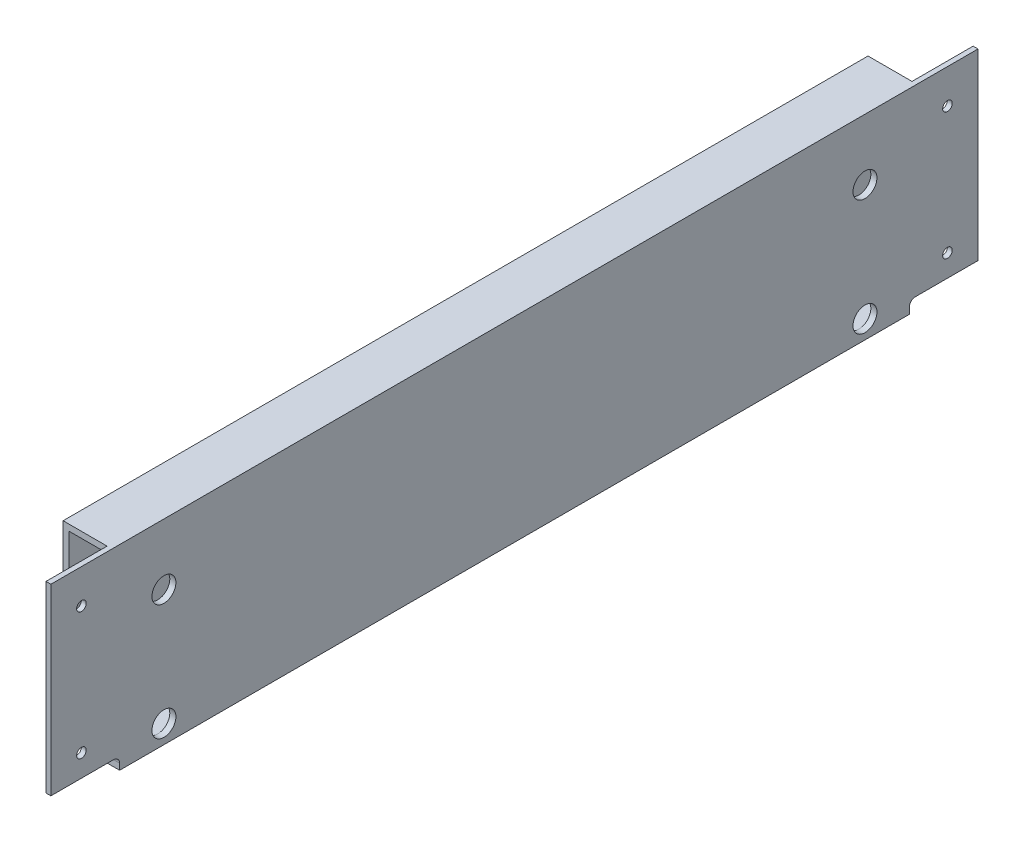
SolidWorks part; units mm, degrees
material "6061-T6 (SS)"
ref_plane "Front Plane" through (0, 0, 0) normal (0, 0, 1) x (1, 0, 0)
ref_plane "Top Plane" through (0, 0, 0) normal (0, 1, 0) x (1, 0, 0)
ref_plane "Right Plane" through (0, 0, 0) normal (1, 0, 0) x (0, 0, -1)
sketch "Sketch1" plane through (0, 0, 0) normal (0, 0, 1) x (1, 0, 0)
  line L0 (-12.7, 50.8) -> (12.7, -50.8) construction
  line L1 (-12.7, 50.8) -> (12.7, 50.8)
  line L2 (-12.7, 50.8) -> (-12.7, -50.8)
  line L3 (-12.7, -50.8) -> (12.7, -50.8)
  line L4 (12.7, 50.8) -> (12.7, -50.8)
  point P4 (0, 0)
  dimension "D1" = 25.4
  dimension "D2" = 101.6
extrude "Extrude-Thin1" add sketch "Sketch1" along normal mid plane 481.75 thin
sketch "Sketch2" plane through (-12.7, 0, 0) normal (-1, 0, 0) x (0, 0, 1)
  line L0 (240.875, 50.8) -> (-240.875, 50.8) construction
  line L1 (209.125, 50.8) -> (240.875, 50.8)
  line L2 (209.125, 50.8) -> (209.125, -50.8)
  line L3 (209.125, -50.8) -> (240.875, -50.8)
  line L4 (240.875, 50.8) -> (240.875, -50.8)
  dimension "D1" = 31.75
extrude "Cut-Extrude1" cut sketch "Sketch2" against normal offset from surface (22.86 mm away) 2.54 up to face at (12.7, 0, 0)
sketch "Sketch3" plane through (-12.7, 0, 0) normal (-1, 0, 0) x (0, 0, 1)
  line L1 (240.875, -44.45) -> (205.1562, -44.45)
  line L2 (240.875, -44.45) -> (240.875, -50.8)
  line L3 (240.875, -50.8) -> (205.1562, -50.8)
  line L4 (205.1562, -44.45) -> (205.1562, -50.8)
  line L5 (240.875, 50.8) -> (240.875, -50.8) construction
  dimension "D1" = 6.35
  dimension "D2" = 35.7188
extrude "Cut-Extrude2" cut sketch "Sketch3" against normal through all
sketch "Sketch4" plane through (10.16, 0, 0) normal (-1, 0, 0) x (0, 0, 1)
  line L0 (0, 0) -> (92.727, 0) construction
  line L1 (225, 44.45) -> (225, 33.02) construction
  line L3 (240.875, -44.45) -> (209.125, -44.45) construction
  point P7 (225, -44.45)
  dimension "D1" = 33.02
hole_wizard "#10 Clearance Hole1" positions "Sketch6" profile "Sketch5" hole size "#10" standard "Ansi Inch" end condition through all
sketch "Sketch6" plane through (10.16, 0, 0) normal (-1, 0, 0) x (0, 0, 1)
  point P0 (225, 33.02)
sketch "Sketch5" plane through (10.16, 33.02, 225) normal (0, 1, 0) x (0, 0, 1)
  line L0 (0, 0) -> (0, 2.54)
  line L1 (0, 2.54) -> (2.4892, 2.54)
  line L2 (2.4892, 2.54) -> (2.4892, 0)
  line L5 (2.4892, 0) -> (0, 0)
  line L11 (0, -6.35) -> (0, 107.95) construction
  dimension "Thru Hole Dia." = 4.9784
  dimension "Thru Hole Depth" = 2.54
mirror "Mirror1" about plane through (0, 0, 0) normal (0, 1, 0) of "#10 Clearance Hole1"
mirror "Mirror2" about plane through (0, 0, 0) normal (0, 0, 1) of "Cut-Extrude1", "Cut-Extrude2", "Mirror1", "#10 Clearance Hole1"
fillet "Fillet1" radius 3.175 4 edges at (11.1125, -44.45, 205.1562) (-11.1125, -44.45, 205.1562) (-11.1125, -44.45, -205.1562) (11.1125, -44.45, -205.1562)
sketch "Sketch7" plane through (9.525, 0, 0) normal (-1, 0, 0) x (0, 0, 1)
  line L0 (182.1375, -41.275) -> (127.8328, -41.275) construction
  line L1 (182.1375, -41.275) -> (182.1375, 19.05) construction
  line L2 (209.125, 47.625) -> (209.125, -44.45) construction
  line L3 (205.1562, -50.8) -> (-205.1562, -50.8) construction
  line L4 (209.125, 50.8) -> (-209.125, 50.8) construction
  circle A0 centre (182.1375, -41.275) radius 6.223
  circle A1 centre (182.1375, 19.05) radius 6.223
  dimension "D3" = 12.446
  dimension "D1" = 26.9875
  dimension "D2" = 9.525
  dimension "D4" = 31.75
extrude "Cut-Extrude3" cut sketch "Sketch7" against normal up to next (3.175 mm away)
hole_wizard "1/4 Clearance Hole1" positions "Sketch9" profile "Sketch8" hole size "1/4" standard "Ansi Inch" end condition up to next
sketch "Sketch9" plane through (-12.7, 25.3344, -55.0281) normal (-1, 0, 0) x (0, 0, 1)
  circle A0 centre (237.1656, -6.2844) radius 6.223 construction
  point P0 (237.1656, -6.2844)
  point P1 (237.1656, -66.6094)
sketch "Sketch8" plane through (-12.7, 19.05, 182.1375) normal (0, 1, 0) x (0, 0, 1)
  line L0 (0, 0) -> (0, 3.175)
  line L1 (0, 3.175) -> (3.8989, 3.175)
  line L2 (3.2639, 2.54) -> (3.2639, 0.635)
  line L3 (3.2639, 0.635) -> (3.8989, 0)
  line L5 (3.8989, 0) -> (0, 0)
  line L6 (-3.2639, 0.635) -> (-3.8989, 0) construction
  line L7 (3.8989, 3.175) -> (3.2639, 2.54)
  line L8 (-3.8989, 3.175) -> (-3.2639, 2.54) construction
  line L11 (0, -6.35) -> (0, 107.95) construction
  dimension "Thru Hole Dia." = 6.5278
  dimension "Thru Hole Depth" = 3.175
  dimension "Near C'Sink Dia." = 7.7978
  dimension "Near C'Sink Angle" = 90
  dimension "Far C'Sink Dia." = 7.7978
  dimension "Far C'Sink Angle" = 90
mirror "Mirror3" about plane through (0, 0, 0) normal (0, 0, 1) of "Cut-Extrude3", "1/4 Clearance Hole1"
